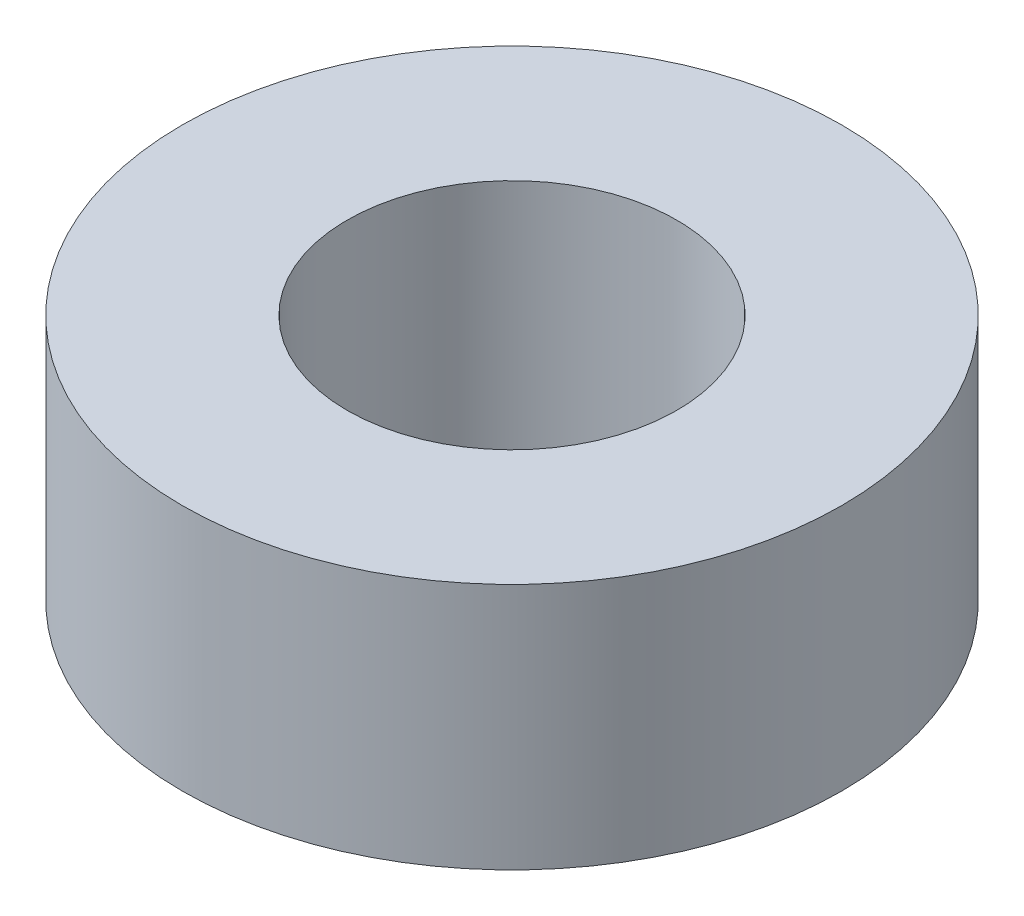
SolidWorks part; units mm, degrees
material "1060 Alloy"
ref_plane "Front Plane" through (0, 0, 0) normal (0, 0, 1) x (1, 0, 0)
ref_plane "Top Plane" through (0, 0, 0) normal (0, 1, 0) x (1, 0, 0)
ref_plane "Right Plane" through (0, 0, 0) normal (1, 0, 0) x (0, 0, -1)
sketch "Sketch1" plane through (0, 0, 0) normal (0, 1, 0) x (1, 0, 0)
  circle A0 centre (0, 0) radius 4
  circle A1 centre (0, 0) radius 2
  dimension "D1" = 8
  dimension "D2" = 4
extrude "Boss-Extrude1" add sketch "Sketch1" along normal blind 3
